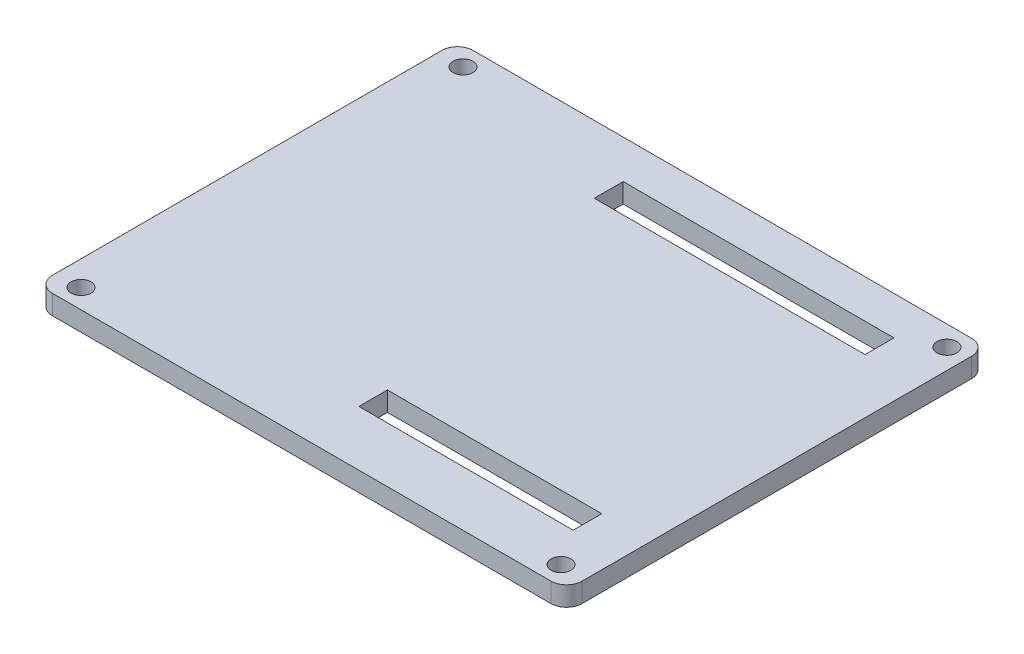
SolidWorks part; units mm, degrees
ref_plane "Front Plane" through (0, 0, 0) normal (0, 0, 1) x (1, 0, 0)
ref_plane "Top Plane" through (0, 0, 0) normal (0, 1, 0) x (1, 0, 0)
ref_plane "Right Plane" through (0, 0, 0) normal (1, 0, 0) x (0, 0, -1)
sketch "Sketch1" plane through (0, 0, 0) normal (0, 1, 0) x (1, 0, 0)
  line L1 (0, 0) -> (86.36, 0)
  line L2 (0, 0) -> (0, -68.58)
  line L3 (0, -68.58) -> (86.36, -68.58)
  line L4 (86.36, 0) -> (86.36, -68.58)
  dimension "D1" = 86.36
  dimension "D2" = 68.58
extrude "Boss-Extrude1" add sketch "Sketch1" along normal blind 3.175
fillet "Fillet1" radius 2.54 4 edges at (0, 1.5875, 68.58) (86.36, 1.5875, 68.58) (86.36, 1.5875, 0) (0, 1.5875, 0)
sketch "Sketch2" plane through (0, 3.175, 0) normal (0, 1, 0) x (-1, 0, 0)
  circle A0 centre (-4.054, 3.1522) radius 1.6129
  circle A1 centre (-83.0761, 3.2839) radius 1.6129
  circle A2 centre (-82.306, 65.4278) radius 1.6129
  circle A3 centre (-4.054, 65.4278) radius 1.6129
extrude "Cut-Extrude1" cut sketch "Sketch2" against normal through all
sketch "Sketch3" plane through (0, 3.175, 0) normal (0, 1, 0) x (1, 0, 0)
  line L0 (33.7814, -6.2779) -> (12.2926, -6.2779) construction
  line L1 (33.2931, -6.2779) -> (77.4391, -6.2779)
  line L2 (33.2931, -6.2779) -> (33.2931, -10.9908)
  line L3 (33.2931, -10.9908) -> (77.4391, -10.9908)
  line L4 (77.4391, -6.2779) -> (77.4391, -10.9908)
  line L5 (12.2926, -59.5779) -> (43.8997, -59.5779) construction
  line L6 (43.506, -59.5779) -> (78.445, -59.5779)
  line L7 (43.506, -59.5779) -> (43.506, -54.9195)
  line L8 (43.506, -54.9195) -> (78.445, -54.9195)
  line L9 (78.445, -59.5779) -> (78.445, -54.9195)
extrude "Cut-Extrude2" cut sketch "Sketch3" against normal through all
